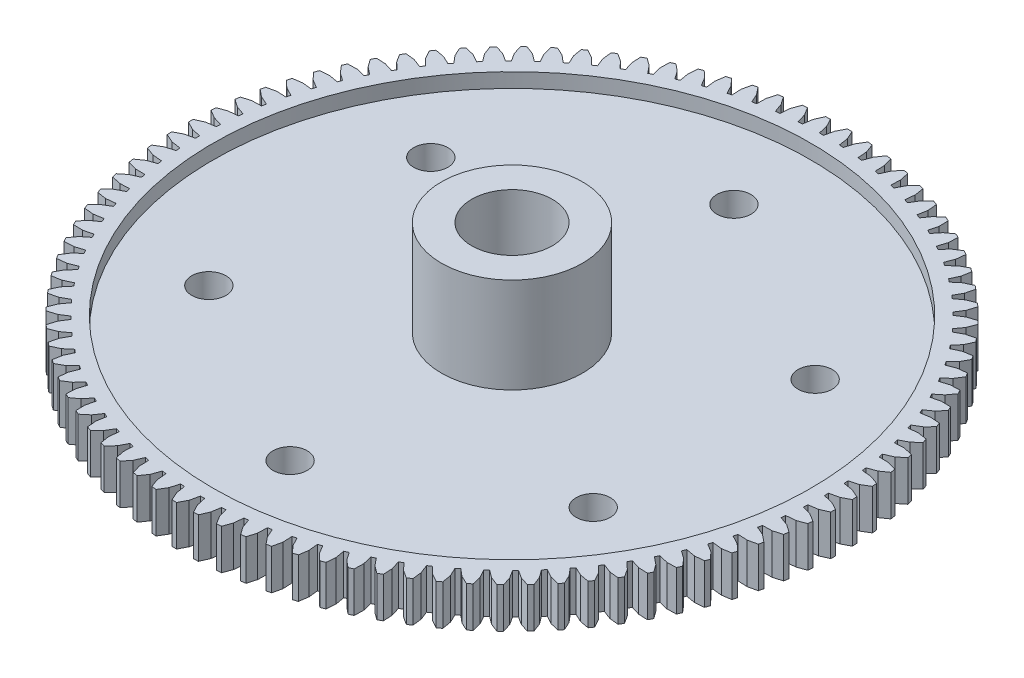
SolidWorks part; units mm, degrees
ref_plane "Front Plane" through (0, 0, 0) normal (0, 0, 1) x (1, 0, 0)
ref_plane "Top Plane" through (0, 0, 0) normal (0, 1, 0) x (1, 0, 0)
ref_plane "Right Plane" through (0, 0, 0) normal (1, 0, 0) x (0, 0, -1)
sketch "Sketch1" plane through (0, 0, 0) normal (0, 1, 0) x (1, 0, 0)
  circle A0 centre (0, 0) radius 25.9334
  dimension "D1" = 51.8668
extrude "Boss-Extrude1" add sketch "Sketch1" along normal blind 3.175
sketch "Sketch2" plane through (0, 3.175, 0) normal (0, 1, 0) x (1, 0, 0)
  circle A0 centre (0, 0) radius 5.5499
  dimension "D1" = 11.0998
extrude "Boss-Extrude2" add sketch "Sketch2" along normal blind 6.35
sketch "Sketch3" plane through (0, 9.525, 0) normal (0, 1, 0) x (1, 0, 0)
  circle A0 centre (0, 0) radius 3.175
  dimension "D1" = 6.35
extrude "Cut-Extrude1" cut sketch "Sketch3" against normal through all
sketch "Sketch4" plane through (0, 3.175, 0) normal (0, 1, 0) x (1, 0, 0)
  circle A0 centre (0, 0) radius 5.5499
  circle A1 centre (0, 0) radius 23.5204
  dimension "D1" = 47.0408
extrude "Cut-Extrude2" cut sketch "Sketch4" against normal blind 1.143
sketch "Sketch5" plane through (0, 3.175, 0) normal (0, 1, 0) x (1, 0, 0)
  line L0 (0, 0) -> (0, 45.2162) construction
  circle A0 centre (0, 17.4625) radius 1.3462
extrude "Cut-Extrude3" cut sketch "Sketch5" against normal through all
pattern_circular "CirPattern1" count 6 over 360 about axis through (0, 0, 0) along (0, 1, 0) of "Cut-Extrude3"
sketch "Sketch6" plane through (0, 3.175, 0) normal (0, 1, 0) x (1, 0, 0)
  line L0 (0, 0) -> (0, 25.9334) construction
  line L1 (-0.3605, 24.5483) -> (-0.0334, 24.5483)
  line L2 (-0.0334, 24.5483) -> (0.4707, 25.9334) construction
  line L3 (-0.3605, 24.5483) -> (-0.8646, 25.9334) construction
  line L4 (0.4707, 25.9334) -> (0.7978, 25.9334) construction
  line L5 (-0.8646, 25.9334) -> (-0.5214, 25.274)
  line L6 (-0.5214, 25.274) -> (-0.3605, 24.5483)
  line L7 (-0.0334, 24.5483) -> (0.1275, 25.274)
  line L8 (0.1275, 25.274) -> (0.4707, 25.9334)
  circle A0 centre (0, 0) radius 25.9334 construction
  dimension "D1" = 70
  dimension "D2" = 70
  dimension "D3" = 165
  dimension "D4" = 165
extrude "Cut-Extrude4" cut sketch "Sketch6" against normal through all flip side to cut
pattern_circular "CirPattern2" count 96 over 360 about axis through (0, 3.175, 0) along (0, -1, 0) of "Cut-Extrude4"
sketch "Pitch Dia" plane through (0, 0, 0) normal (0, -1, 0) x (1, 0, 0)
  circle A0 centre (0, 0) radius 25.4
  dimension "D1" = 50.8
